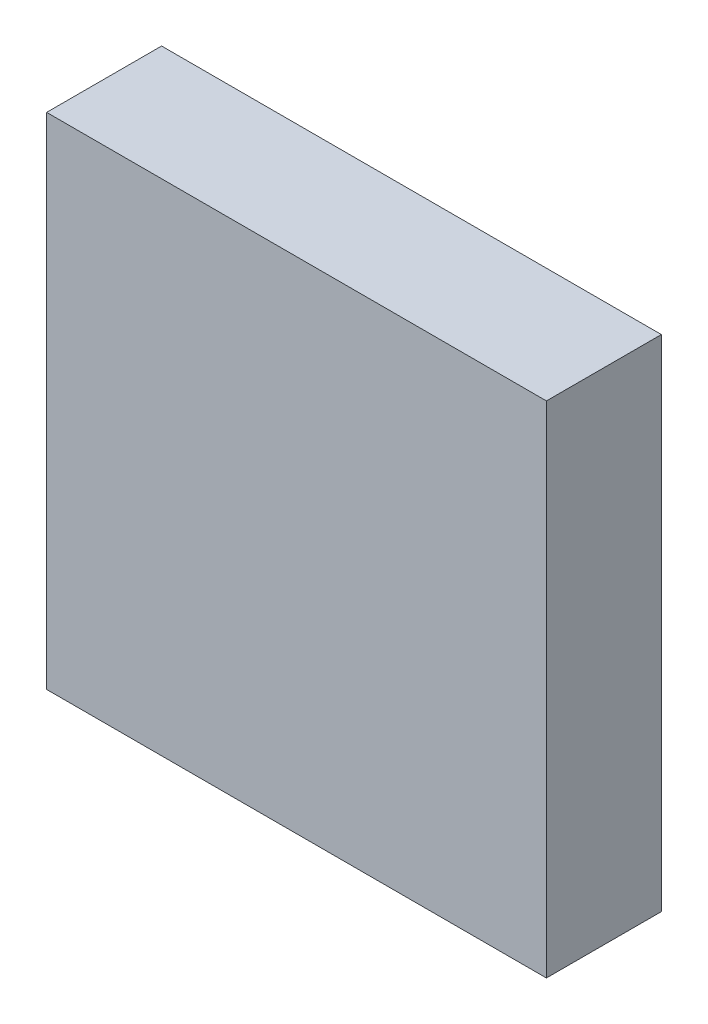
SolidWorks part; units mm, degrees
ref_plane "前视基准面" through (0, 0, 0) normal (0, 0, 1) x (1, 0, 0)
ref_plane "上视基准面" through (0, 0, 0) normal (0, 1, 0) x (1, 0, 0)
ref_plane "右视基准面" through (0, 0, 0) normal (1, 0, 0) x (0, 0, -1)
sketch "草图1" plane through (0, 0, 0) normal (0, 0, 1) x (1, 0, 0)
  line L0 (34.0429, 24.6253) -> (47.3119, 24.6253) construction
  line L1 (35.4992, 19.6253) -> (45.4992, 19.6253)
  line L2 (35.4992, 29.6253) -> (45.4992, 29.6253)
  line L3 (40.4992, 30.7096) -> (40.4992, 17.5729) construction
  line L4 (35.4992, 29.6253) -> (35.4992, 19.6253)
  line L5 (45.4992, 29.6253) -> (45.4992, 19.6253)
  dimension "D1" = 10
  dimension "D2" = 10
extrude "凸台-拉伸1" add sketch "草图1" along normal blind 2.3
